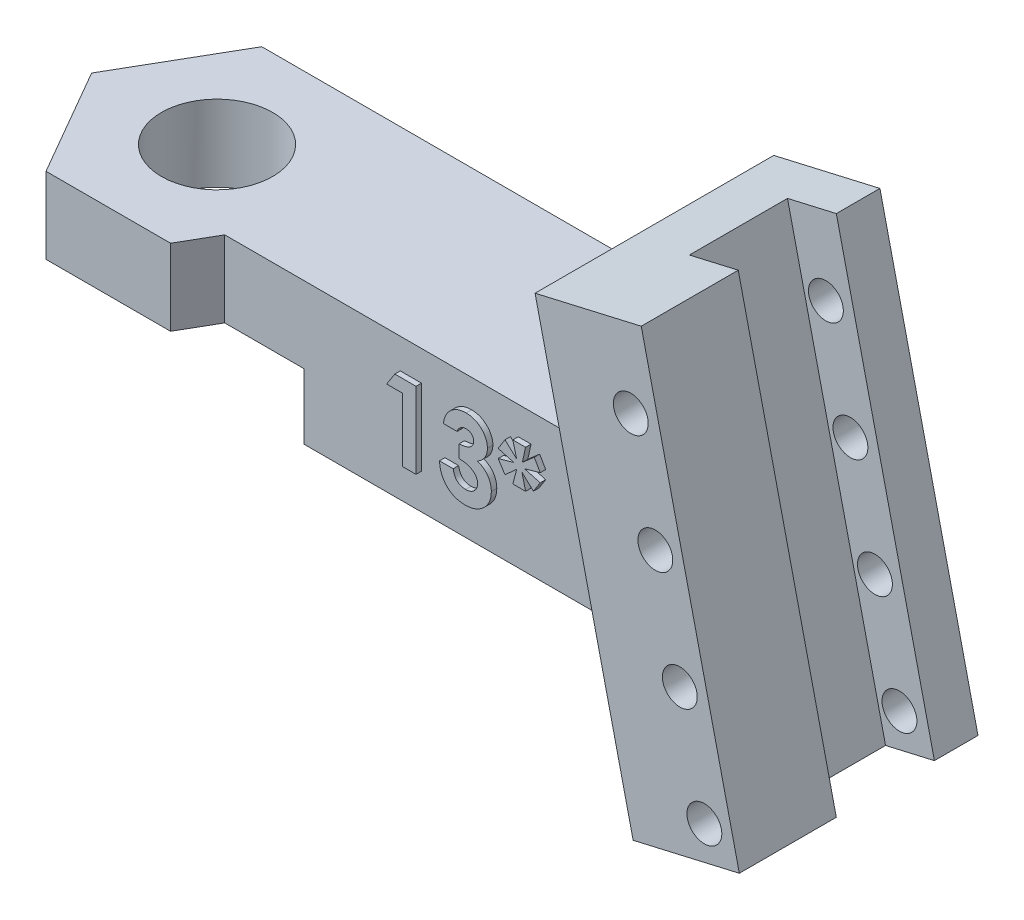
SolidWorks part; units mm, degrees
ref_plane "Front Plane" through (0, 0, 0) normal (0, 0, 1) x (1, 0, 0)
ref_plane "Top Plane" through (0, 0, 0) normal (0, 1, 0) x (1, 0, 0)
ref_plane "Right Plane" through (0, 0, 0) normal (1, 0, 0) x (0, 0, -1)
sketch "Sketch1" plane through (0, 0, 0) normal (0, 1, 0) x (1, 0, 0)
  line L1 (0, 0) -> (25, 0)
  line L2 (0, 0) -> (0, -6.75)
  line L3 (0, -6.75) -> (25, -6.75)
  line L4 (25, 0) -> (25, -6.75)
  dimension "D1" = 6.75
  dimension "D2" = 25
extrude "Boss-Extrude1" add sketch "Sketch1" along normal blind 6.5
ref_plane "Plane1" through (0, 0, 3.375) normal (0, 0, 1) x (1, 0, 0)
sketch "Sketch5" plane through (0, 6.5, 0) normal (0, 1, 0) x (1, 0, 0)
  line L0 (0, 0) -> (0, -6.75) construction
  line L1 (-5.7158, -3.375) -> (-2.8579, -8.325)
  line L2 (-2.8579, -8.325) -> (2.8579, -8.325)
  line L3 (2.8579, -8.325) -> (5.7158, -3.375)
  line L4 (5.7158, -3.375) -> (2.8579, 1.575)
  line L5 (2.8579, 1.575) -> (-2.8579, 1.575)
  line L6 (-2.8579, 1.575) -> (-5.7158, -3.375)
  circle A0 centre (0, -3.375) radius 4.95 construction
  dimension "D1" = 4.95
extrude "Boss-Extrude4" add sketch "Sketch5" against normal up to surface (6.5 mm away) up to face at (12.5, 0, 3.375)
sketch "Sketch3" plane through (0, 0, 3.375) normal (0, 0, 1) x (1, 0, 0)
  line L0 (20.6291, 13.925) -> (25.501, 15.0498)
  line L1 (25.501, 15.0498) -> (30, -4.4376)
  line L2 (30, -4.4376) -> (25.1281, -5.5624)
  line L3 (25.1281, -5.5624) -> (20.6291, 13.925)
  line L4 (3.7672, 6.5) -> (25, 6.5) construction
  point P6 (27.5641, -5)
  dimension "D1" = 30
  dimension "D2" = 5
  dimension "D3" = 20
  dimension "D4" = 77
  dimension "D6" = 5
extrude "Boss-Extrude3" add sketch "Sketch3" against normal up to surface (4.95 mm away) and the other way blind 6 up to face at (0, 3.25, -1.575)
sketch "Sketch4" plane through (-2.0083, 8.6988, 0) normal (-0.225, 0.9744, 0) x (0.9744, 0.225, 0)
  line L0 (28.2329, -9.375) -> (28.2329, 1.575) construction
  line L1 (25.9329, -0.425) -> (28.2329, -0.425)
  line L2 (25.9329, -0.425) -> (25.9329, -4.925)
  line L3 (25.9329, -4.925) -> (28.2329, -4.925)
  line L4 (28.2329, -0.425) -> (28.2329, -4.925)
  line L6 (28.2329, 1.575) -> (23.2329, 1.575) construction
  dimension "D1" = 4.5
  dimension "D2" = 2.3
  dimension "D3" = 2
extrude "Cut-Extrude1" cut sketch "Sketch4" against normal blind 23 contours L2 L3 L4 L1
sketch "Sketch6" plane through (0, 6.5, 0) normal (0, 1, 0) x (1, 0, 0)
  circle A0 centre (0, -3.3356) radius 2.55
  dimension "D1" = 5.1
extrude "Cut-Extrude2" cut sketch "Sketch6" against normal blind 10
sketch "Sketch7" plane through (0, 0, -1.575) normal (0, 0, -1) x (-1, 0, 0)
  line L0 (-2.8579, 0) -> (-23.844, 0)
  line L1 (-23.844, 0) -> (-25.1281, -5.5624)
  line L2 (-25.1281, -5.5624) -> (-30, -4.4376)
  line L3 (-30, -4.4376) -> (-25.501, 15.0498)
  line L4 (-25.501, 15.0498) -> (-20.6291, 13.925)
  line L5 (-20.6291, 13.925) -> (-22.3433, 6.5)
  line L6 (-22.3433, 6.5) -> (-2.8579, 6.5)
  line L7 (-2.8579, 6.5) -> (-2.8579, 0)
  dimension "D1" = 20
extrude "Boss-Extrude5" add sketch "Sketch7" against normal up to surface (1.575 mm away) up to face at (13.4304, 3.25, 0)
sketch "Sketch8" plane through (0, 0, 0) normal (0, -1, 0) x (-1, 0, 0)
  line L1 (-4.6765, -11.475) -> (4.6765, -11.475)
  line L2 (4.6765, -11.475) -> (9.3531, -3.375)
  line L3 (9.3531, -3.375) -> (4.6765, 4.725)
  line L4 (4.6765, 4.725) -> (-4.6765, 4.725)
  line L5 (-4.6765, 4.725) -> (-9.3531, -3.375)
  line L6 (-9.3531, -3.375) -> (-4.6765, -11.475)
  circle A0 centre (0, -3.375) radius 8.1 construction
  dimension "D1" = 16.2
extrude "Cut-Extrude3" cut sketch "Sketch8" against normal blind 3
sketch "Sketch9" plane through (0, 0, -1.575) normal (0, 0, -1) x (-1, 0, 0)
  line L0 (-30, -4.4376) -> (-25.501, 15.0498) construction
  line L1 (-25.1281, -5.5624) -> (-30, -4.4376) construction
  line L2 (-28.3959, -3.2685) -> (-25.0216, 11.347) construction
  line L3 (-30, -4.4376) -> (-25.501, 15.0498) construction
  circle A0 centre (-28.3959, -3.2685) radius 0.8
  circle A4 centre (-27.2711, 1.6033) radius 0.8
  circle A5 centre (-26.1464, 6.4752) radius 0.8
  circle A6 centre (-25.0216, 11.347) radius 0.8
  dimension "D1" = 1.6
  dimension "D2" = 1.3
  dimension "D5" = 5
  dimension "D3" = 1.5
  dimension "D4" = 5
  dimension "D6" = 5
extrude "Cut-Extrude4" cut sketch "Sketch9" against normal up to surface (10.95 mm away) up to face at (25.3146, 4.7437, 9.375)
sketch "Sketch10" plane through (0, 0, 6.75) normal (0, 0, 1) x (1, 0, 0)
  text T0 "<b>13*</b>"
extrude "Boss-Extrude6" add sketch "Sketch10" along normal blind 0.25
